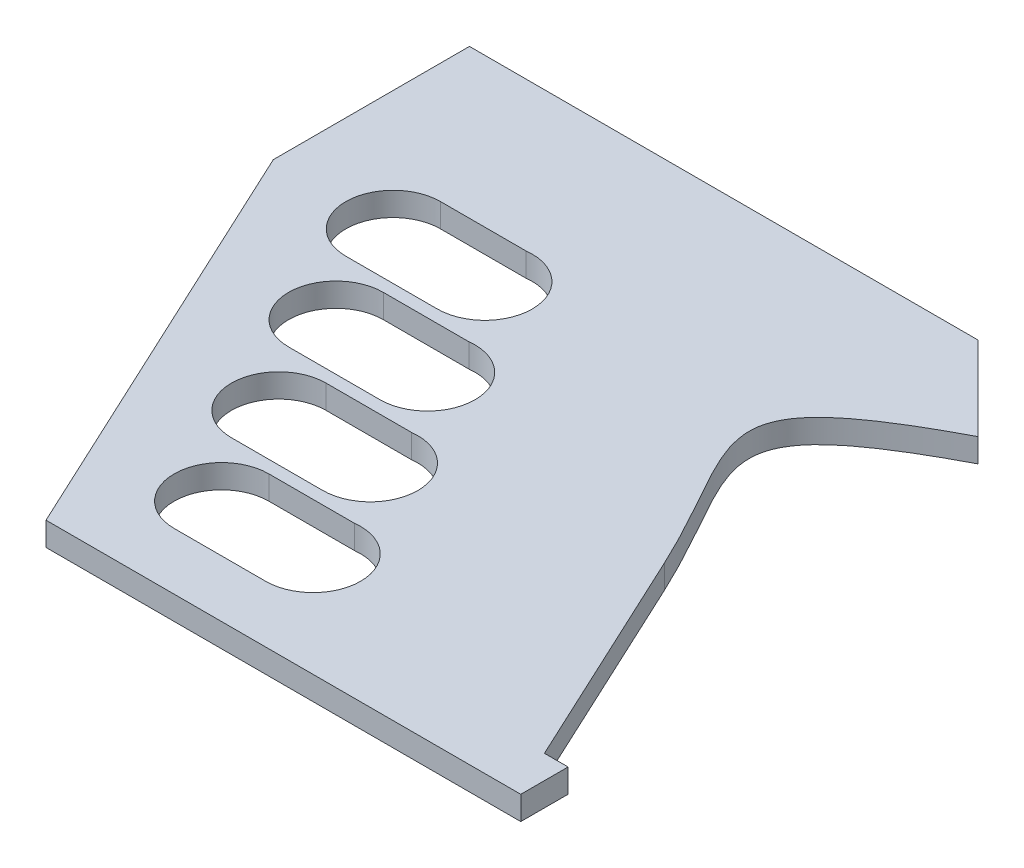
SolidWorks part; units mm, degrees
ref_plane "Front Plane" through (0, 0, 0) normal (0, 0, 1) x (1, 0, 0)
ref_plane "Top Plane" through (0, 0, 0) normal (0, 1, 0) x (1, 0, 0)
ref_plane "Right Plane" through (0, 0, 0) normal (1, 0, 0) x (0, 0, -1)
sketch "Sketch1" plane through (0, 0, 0) normal (0, 1, 0) x (1, 0, 0)
  line L0 (29.424, 17.6777) -> (-78.0526, 17.6777)
  line L1 (29.424, 17.6777) -> (47.1017, 0)
  line L2 (-78.0526, 17.6777) -> (-78.0526, -23.78)
  line L3 (-78.0526, -23.78) -> (-36.0849, -113.78)
  line L4 (-36.0849, -113.78) -> (64.252, -113.78)
  line L5 (64.252, -113.78) -> (64.252, -103.78)
  line L6 (64.252, -103.78) -> (59.252, -103.78)
  line L7 (59.252, -103.78) -> (37.1044, -56.2842)
  line L8 (47.1017, 0) -> (-78.0526, 0) construction
  line L9 (21.9474, 0) -> (21.9474, -23.78) construction
  line L10 (37.1044, -56.2842) -> (10.8586, 0) construction
  line L11 (39.5648, -61.5607) -> (28.8445, -38.5709) construction
  line L12 (-78.0526, -23.78) -> (21.9474, -23.78) construction
  spline S0 degree 3 poles (47.1017, 0) (7.9164, -20.533) (22.6076, -25.1958) (37.1044, -56.2842) knots 0 0 0 0 1 1 1 1
  dimension "D1" = 90
  dimension "D2" = 10
  dimension "D3" = 5
  dimension "D4" = 115
  dimension "D5" = 25
  dimension "D6" = 45
  dimension "D7" = 100
extrude "Boss-Extrude1" add sketch "Sketch1" along normal blind 5
sketch "Sketch2" plane through (0, 5, 0) normal (0, 1, 0) x (1, 0, 0)
  line L0 (-52.7157, -13.78) -> (-42.7157, -13.78)
  line L1 (-43.3895, -33.78) -> (-33.3895, -33.78)
  line L2 (-52.7157, -13.78) -> (-43.3895, -33.78) construction
  line L3 (-42.7157, -13.78) -> (-33.3895, -33.78) construction
  line L4 (-78.0526, -23.78) -> (-36.0849, -113.78) construction
  line L5 (-52.7157, -33.78) -> (-43.3895, -33.78)
  line L6 (-42.7157, -13.78) -> (-34.6105, -13.78)
  line L7 (-78.0526, -23.78) -> (21.9474, -23.78) construction
  arc A0 (-52.7157, -13.78) -> (-52.7157, -33.78) centre (-52.7157, -23.78) ccw
  arc A1 (-33.3895, -33.78) -> (-34.6105, -13.78) centre (-33.3895, -23.7427) ccw
  spline S0 degree 3 poles (37.1044, -56.2842) (22.6076, -25.1958) (7.9164, -20.533) (47.1017, 0) knots 0 0 0 0 1 1 1 1 construction
  point P15 (-48.0526, -23.78)
  point P16 (-38.0526, -23.78)
  dimension "D1" = 20
  dimension "D2" = 10
  dimension "D3" = 30
extrude "Cut-Extrude1" cut sketch "Sketch2" against normal blind 5
pattern_curve "CrvPattern1" of "Cut-Extrude1" along edge at (-57.0687, 5, 68.78) parameters "D1"=4, "D3"=25, "D2"=1, "D4"=10
